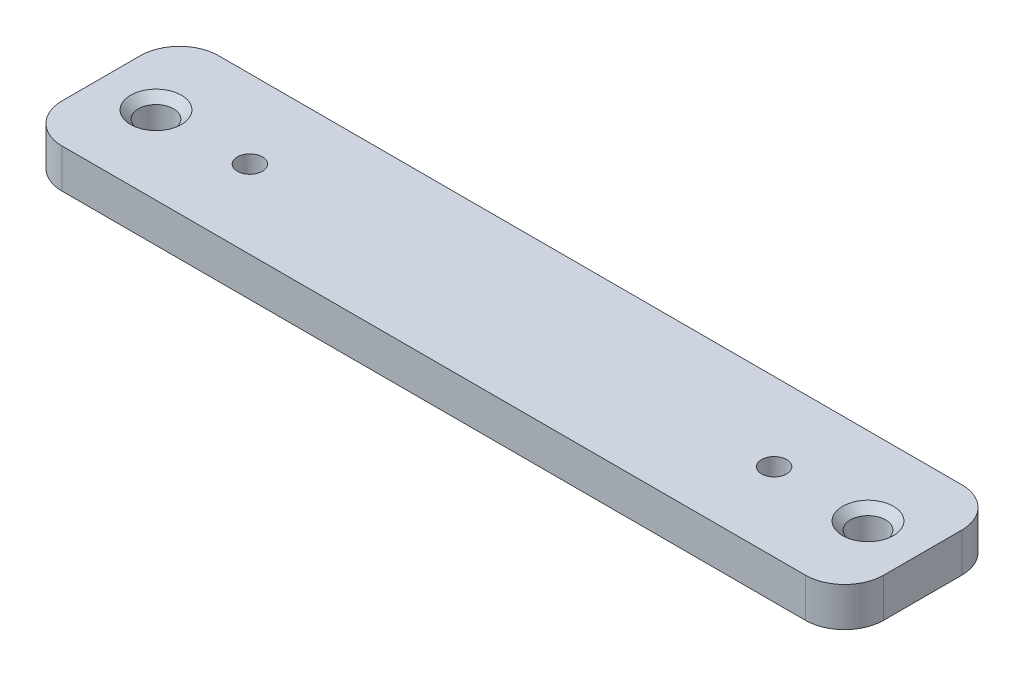
SolidWorks part; units mm, degrees
material "PBT Общее назначение"
ref_plane "Спереди" through (0, 0, 0) normal (0, 0, 1) x (1, 0, 0)
ref_plane "Сверху" through (0, 0, 0) normal (0, 1, 0) x (1, 0, 0)
ref_plane "Справа" through (0, 0, 0) normal (1, 0, 0) x (0, 0, -1)
sketch "Эскиз1" plane through (0, 0, 0) normal (0, 1, 0) x (1, 0, 0)
  line L0 (0, 0) -> (105, 0)
  line L1 (0, 0) -> (0, 20)
  line L2 (105, 0) -> (105, 20)
  line L3 (0, 20) -> (105, 20)
  line L4 (0, 10) -> (105, 10) construction
  line L5 (52.5, 20) -> (52.5, 0) construction
  line L6 (19, 8.4) -> (86, 8.4) construction
  line L7 (7, 7.75) -> (98, 7.75) construction
  circle A0 centre (19, 10) radius 1.6
  circle A1 centre (86, 10) radius 1.6
  circle A2 centre (7, 10) radius 2.25
  circle A3 centre (98, 10) radius 2.25
  point P15 (52.5, 8.4)
  point P22 (52.5, 7.75)
  dimension "D3" = 67
  dimension "D4" = 3.2
  dimension "D5" = 4.5
  dimension "D6" = 7
  dimension "D1" = 20
  dimension "D2" = 105
extrude "Бобышка-Вытянуть1" add sketch "Эскиз1" along normal blind 5
fillet "Скругление2" radius 5 4 edges at (0, 2.5, -20) (0, 2.5, 0) (105, 2.5, -20) (105, 2.5, 0)
chamfer "Фаска1" distance 1 angle 45 2 edges at (98, 5, -7.75) (7, 5, -7.75)
chamfer "Фаска2" distance 1 angle 45 2 edges at (86, 0, -8.4) (19, 0, -8.4)
